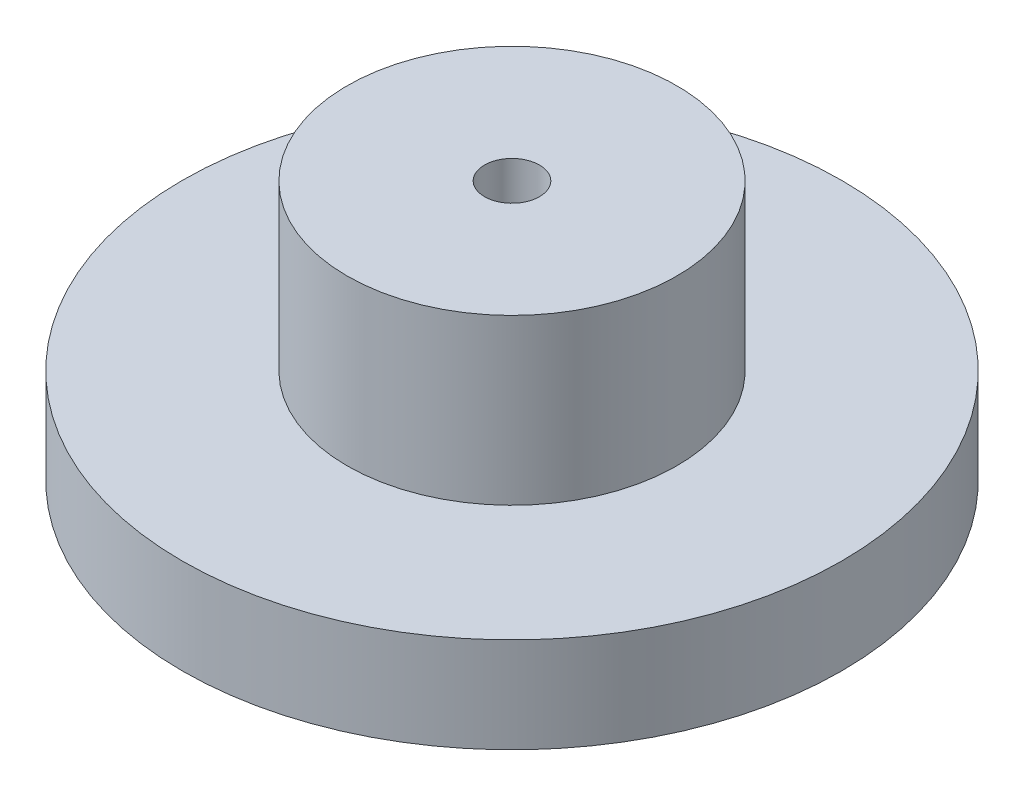
SolidWorks part; units mm, degrees
material "Acier non allié"
ref_plane "Plan de face" through (0, 0, 0) normal (0, 0, 1) x (1, 0, 0)
ref_plane "Plan de dessus" through (0, 0, 0) normal (0, 1, 0) x (1, 0, 0)
ref_plane "Plan de droite" through (0, 0, 0) normal (1, 0, 0) x (0, 0, -1)
sketch "Esquisse1" plane through (0, 0, 0) normal (0, 1, 0) x (1, 0, 0)
  circle A0 centre (0, 0) radius 38.1
  dimension "D1" = 76.2
extrude "Boss.-Extru.1" add sketch "Esquisse1" along normal blind 11
sketch "Esquisse2" plane through (0, 11, 0) normal (0, 1, 0) x (1, 0, 0)
  circle A0 centre (0, 0) radius 19.05
  dimension "D1" = 38.1
extrude "Boss.-Extru.2" add sketch "Esquisse2" along normal blind 19
sketch "Esquisse3" plane through (0, 30, 0) normal (0, 1, 0) x (1, 0, 0)
  circle A0 centre (0, 0) radius 3.175
  dimension "D1" = 6.35
extrude "Enlèv. mat.-Extru.1" cut sketch "Esquisse3" against normal through all
